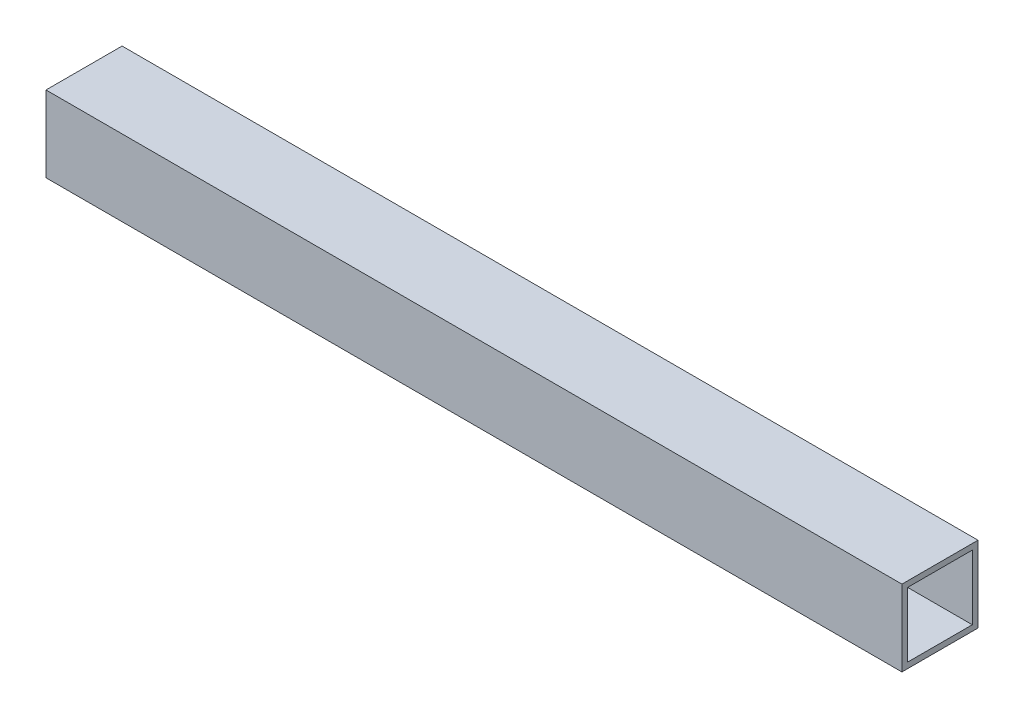
SolidWorks part; units mm, degrees
ref_plane "Front Plane" through (0, 0, 0) normal (0, 0, 1) x (1, 0, 0)
ref_plane "Top Plane" through (0, 0, 0) normal (0, 1, 0) x (1, 0, 0)
ref_plane "Right Plane" through (0, 0, 0) normal (1, 0, 0) x (0, 0, -1)
sketch "Sketch1" plane through (0, 0, 0) normal (0, 0, 1) x (1, 0, 0)
  line L1 (225, -20) -> (-225, -20)
  line L2 (225, -20) -> (225, 20)
  line L3 (225, 20) -> (-225, 20)
  line L4 (-225, -20) -> (-225, 20)
  line L5 (225, -20) -> (-225, 20) construction
  line L6 (225, 20) -> (-225, -20) construction
  point P0 (0, 0)
  dimension "D1" = 450
  dimension "D2" = 40
extrude "Boss-Extrude1" add sketch "Sketch1" along normal blind 40
sketch "Sketch2" plane through (225, 0, 0) normal (1, 0, 0) x (0, 0, -1)
  line L8 (-3, -17) -> (-3, 17)
  line L9 (-3, 17) -> (-37, 17)
  line L10 (-37, 17) -> (-37, -17)
  line L11 (-37, -17) -> (-3, -17)
  line L12 (-3, -17) -> (-3, 17)
  line L13 (-3, 17) -> (-37, 17)
  line L14 (-37, 17) -> (-37, -17)
  line L15 (-37, -17) -> (-3, -17)
  dimension "D1" = 3
extrude "Cut-Extrude1" cut sketch "Sketch2" against normal through all
